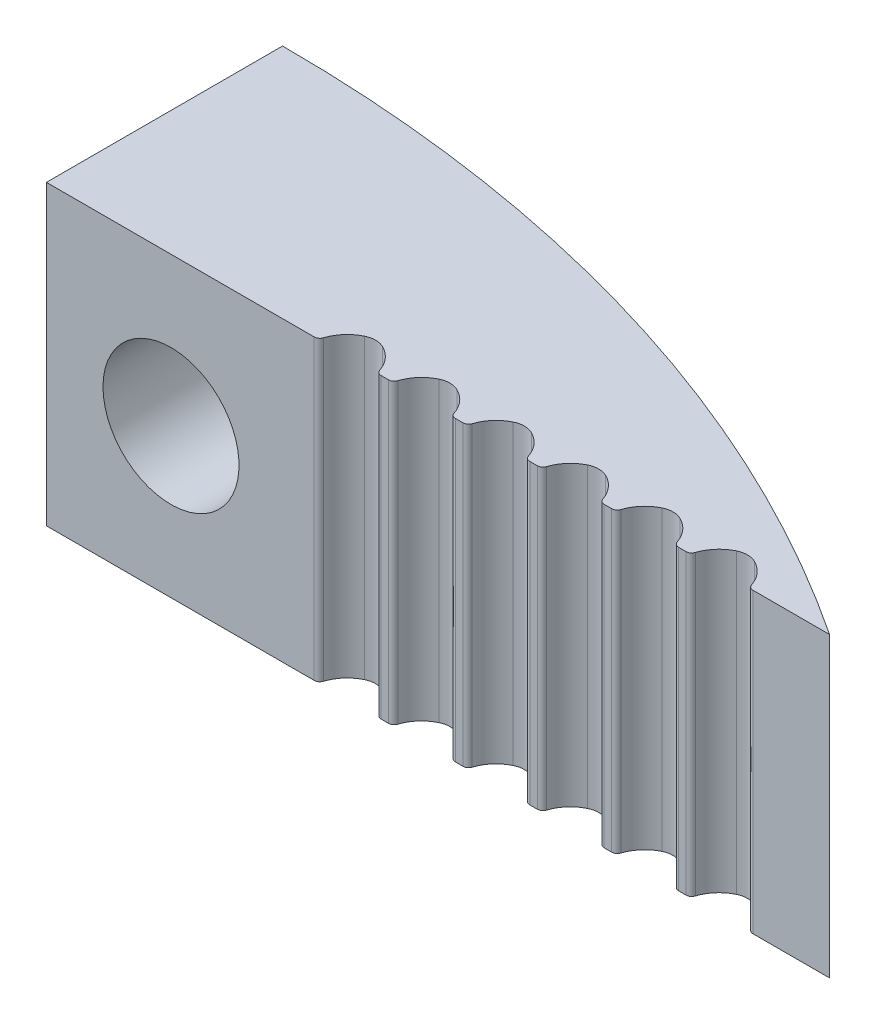
SolidWorks part; units mm, degrees
ref_plane "Front Plane" through (0, 0, 0) normal (0, 0, 1) x (1, 0, 0)
ref_plane "Top Plane" through (0, 0, 0) normal (0, 1, 0) x (1, 0, 0)
ref_plane "Right Plane" through (0, 0, 0) normal (1, 0, 0) x (0, 0, -1)
sketch "Sketch1" plane through (0, 0, 0) normal (0, 1, 0) x (1, 0, 0)
  line L0 (0, 0) -> (0, 6.35)
  line L1 (0, 0) -> (21.0606, 0)
  arc A0 (0, 6.35) -> (21.0606, 0) centre (0, -31.75) cw
  dimension "D1" = 38.1
  dimension "D2" = 6.35
extrude "Boss-Extrude1" add sketch "Sketch1" along normal blind 8 contours L0 A0 L1
ref_plane "Plane1" through (0, 0, -6.35) normal (0, 0, -1) x (-1, 0, 0)
hole_wizard "CBORE for #6 Socket Head Cap Screw1" positions "Sketch5" profile "Sketch7" counterbore size "#6" standard "ANSI Inch" end condition through all
sketch "Sketch5" plane through (0, 0, -6.35) normal (0, 0, -1) x (-1, 0, 0)
  line L0 (0, 8) -> (-6.7, 0)
  point P0 (-3.35, 4)
  point P11 (-3.35, 4)
  dimension "D1" = 6.7
sketch "Sketch7" plane through (3.35, 4, -6.35) normal (1, 0, 0) x (0, 1, 0)
  line L0 (0, 0) -> (0, 6.35)
  line L1 (0, 6.35) -> (1.8288, 6.35)
  line L3 (1.8288, 6.35) -> (1.8288, 3.5052)
  line L4 (1.8288, 3.5052) -> (3.175, 3.5052)
  line L5 (3.175, 3.5052) -> (3.175, 0)
  line L7 (3.175, 0) -> (0, 0)
  line L11 (0, -6.35) -> (0, 107.95) construction
  dimension "Thru Hole Dia." = 3.6576
  dimension "Thru Hole Depth" = 6.35
  dimension "C'Bore Dia." = 6.35
  dimension "C'Bore Depth" = 3.5052
sketch "Sketch8" plane through (0, 0, 0) normal (0, -1, 0) x (1, 0, 0)
  line L0 (7.2023, 0) -> (7, 0)
  line L1 (7, 0) -> (0, 0)
  line L2 (0, 0) -> (21.0606, 0) construction
  line L3 (9.2023, 0) -> (9, 0)
  line L4 (11.2023, 0) -> (11, 0)
  line L5 (13.2023, 0) -> (13, 0)
  line L6 (15.2023, 0) -> (15, 0)
  line L7 (17.2023, 0) -> (17, 0)
  line L8 (19, 0) -> (19, 1.3967)
  line L9 (19, 1.3967) -> (7, 1.3967)
  line L10 (7, 1.3967) -> (7, 0)
  arc A0 (7.858, -0.6939) -> (8.3444, -0.6939) centre (8.1012, -0.195) ccw
  arc A1 (7.858, -0.6939) -> (7.345, -0.1037) centre (8.2962, 0.205) cw
  arc A2 (8.3444, -0.6939) -> (8.8573, -0.1037) centre (7.9062, 0.205) ccw
  arc A3 (8.8573, -0.1037) -> (9, 0) centre (9, -0.15) cw
  arc A4 (7.345, -0.1037) -> (7.2023, 0) centre (7.2023, -0.15) ccw
  arc A5 (9.858, -0.6939) -> (10.3444, -0.6939) centre (10.1012, -0.195) ccw
  arc A6 (9.858, -0.6939) -> (9.345, -0.1037) centre (10.2962, 0.205) cw
  arc A7 (10.3444, -0.6939) -> (10.8573, -0.1037) centre (9.9062, 0.205) ccw
  arc A8 (10.8573, -0.1037) -> (11, 0) centre (11, -0.15) cw
  arc A9 (9.345, -0.1037) -> (9.2023, 0) centre (9.2023, -0.15) ccw
  arc A10 (11.858, -0.6939) -> (12.3444, -0.6939) centre (12.1012, -0.195) ccw
  arc A11 (11.858, -0.6939) -> (11.345, -0.1037) centre (12.2962, 0.205) cw
  arc A12 (12.3444, -0.6939) -> (12.8573, -0.1037) centre (11.9062, 0.205) ccw
  arc A13 (12.8573, -0.1037) -> (13, 0) centre (13, -0.15) cw
  arc A14 (11.345, -0.1037) -> (11.2023, 0) centre (11.2023, -0.15) ccw
  arc A15 (13.858, -0.6939) -> (14.3444, -0.6939) centre (14.1012, -0.195) ccw
  arc A16 (13.858, -0.6939) -> (13.345, -0.1037) centre (14.2962, 0.205) cw
  arc A17 (14.3444, -0.6939) -> (14.8573, -0.1037) centre (13.9062, 0.205) ccw
  arc A18 (14.8573, -0.1037) -> (15, 0) centre (15, -0.15) cw
  arc A19 (13.345, -0.1037) -> (13.2023, 0) centre (13.2023, -0.15) ccw
  arc A20 (15.858, -0.6939) -> (16.3444, -0.6939) centre (16.1012, -0.195) ccw
  arc A21 (15.858, -0.6939) -> (15.345, -0.1037) centre (16.2962, 0.205) cw
  arc A22 (16.3444, -0.6939) -> (16.8573, -0.1037) centre (15.9062, 0.205) ccw
  arc A23 (16.8573, -0.1037) -> (17, 0) centre (17, -0.15) cw
  arc A24 (15.345, -0.1037) -> (15.2023, 0) centre (15.2023, -0.15) ccw
  arc A25 (17.858, -0.6939) -> (18.3444, -0.6939) centre (18.1012, -0.195) ccw
  arc A26 (17.858, -0.6939) -> (17.345, -0.1037) centre (18.2962, 0.205) cw
  arc A27 (18.3444, -0.6939) -> (18.8573, -0.1037) centre (17.9062, 0.205) ccw
  arc A28 (18.8573, -0.1037) -> (19, 0) centre (19, -0.15) cw
  arc A29 (17.345, -0.1037) -> (17.2023, 0) centre (17.2023, -0.15) ccw
  point P11 (8.1012, -0.75)
  point P27 (10.1012, -0.75)
  point P40 (12.1012, -0.75)
  point P53 (14.1012, -0.75)
  point P66 (16.1012, -0.75)
  point P79 (18.1012, -0.75)
  dimension "D1" = 0.555
  dimension "D2" = 1
  dimension "D3" = 0.4
  dimension "D4" = 2
  dimension "D5" = 0.15
  dimension "D6" = 0.75
  dimension "D7" = 7
  dimension "D8" = 6
extrude "Cut-Extrude1" cut sketch "Sketch8" against normal through all contours L0 A4 A1 A0 A2 A3 L3 A9 A6 A5 A7 A8 L4 A14 A11 A10 A12 A13 L5 A19 A16 A15 A17 A18 L6 A24 A21 A20 A22 A23 L7 A29 A26 A25 A27 A28 L8 L9 L10
